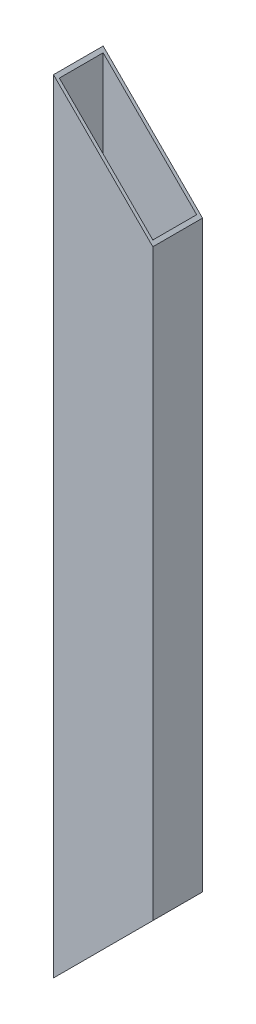
SolidWorks part; units mm, degrees
material "AISI 1015 Acero estirado en frío (SS)"
ref_plane "Alzado" through (0, 0, 0) normal (0, 0, 1) x (1, 0, 0)
ref_plane "Planta" through (0, 0, 0) normal (0, 1, 0) x (1, 0, 0)
ref_plane "Vista lateral" through (0, 0, 0) normal (1, 0, 0) x (0, 0, -1)
sketch "Croquis1" plane through (0, 0, 0) normal (0, 1, 0) x (1, 0, 0)
  line L0 (-23.9, 11.2) -> (23.9, 11.2)
  line L1 (-25.4, -12.7) -> (25.4, -12.7)
  line L2 (-25.4, -12.7) -> (-25.4, 12.7)
  line L3 (-25.4, 12.7) -> (25.4, 12.7)
  line L4 (25.4, -12.7) -> (25.4, 12.7)
  line L5 (-25.4, -12.7) -> (25.4, 12.7) construction
  line L6 (-25.4, 12.7) -> (25.4, -12.7) construction
  line L7 (23.9, -11.2) -> (23.9, 11.2)
  line L8 (-23.9, -11.2) -> (23.9, -11.2)
  line L9 (-23.9, -11.2) -> (-23.9, 11.2)
  point P0 (0, 0)
  dimension "D1" = 25.4
  dimension "D2" = 50.8
  dimension "D3" = 1.5
extrude "Saliente-Extruir1" add sketch "Croquis1" along normal blind 400
ref_plane "Plano1" through (0, 0, 12.7) normal (0, 0, 1) x (1, 0, 0)
sketch "Croquis2" plane through (0, 0, 12.7) normal (0, 0, 1) x (1, 0, 0)
  line L0 (-25.4, 200) -> (88.5987, 200) construction
  line L1 (-25.4, 400) -> (-25.4, 0) construction
  line L2 (-25.4, 0) -> (25.4, 50.8)
  line L3 (25.4, 400) -> (25.4, 0) construction
  line L4 (-25.4, 0) -> (25.4, 0) construction
  line L5 (25.4, 50.8) -> (25.4, 0)
  line L6 (25.4, 0) -> (-25.4, 0)
  line L7 (25.4, 400) -> (-25.4, 400)
  line L8 (25.4, 349.2) -> (25.4, 400)
  line L9 (-25.4, 400) -> (25.4, 349.2)
  dimension "D1" = 45
extrude "Cortar-Extruir1" cut sketch "Croquis2" against normal blind 26
